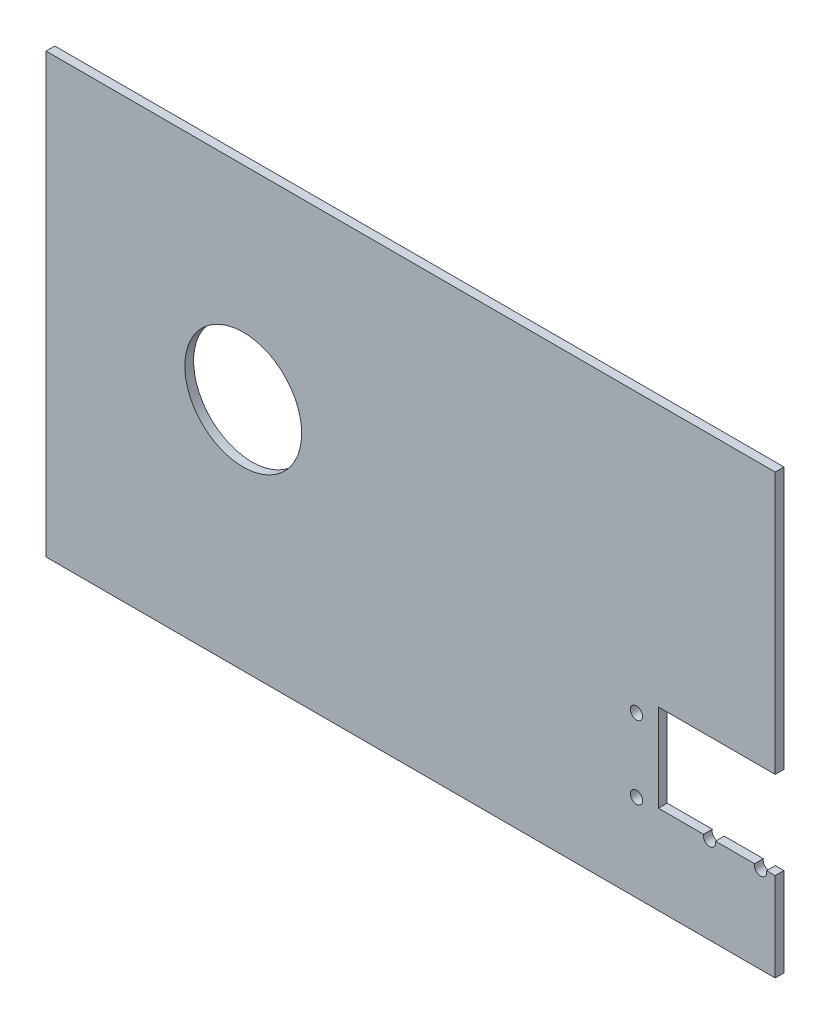
SolidWorks part; units mm, degrees
ref_plane "Front Plane" through (0, 0, 0) normal (0, 0, 1) x (1, 0, 0)
ref_plane "Top Plane" through (0, 0, 0) normal (0, 1, 0) x (1, 0, 0)
ref_plane "Right Plane" through (0, 0, 0) normal (1, 0, 0) x (0, 0, -1)
sketch "Sketch1" plane through (0, 0, 0) normal (0, 0, 1) x (1, 0, 0)
  line L1 (0, 0) -> (249.6, 0)
  line L2 (0, 0) -> (0, -150)
  line L3 (0, -150) -> (249.6, -150)
  line L4 (249.6, 0) -> (249.6, -150)
  dimension "D1" = 150
  dimension "D2" = 249.6
extrude "Boss-Extrude1" add sketch "Sketch1" along normal blind 3
sketch "Sketch2" plane through (0, 0, 3) normal (0, 0, 1) x (1, 0, 0)
  circle A0 centre (67.5, -69.5849) radius 20
  dimension "D1" = 40
extrude "Cut-Extrude1" cut sketch "Sketch2" against normal through all
sketch "Sketch3" plane through (0, 0, 3) normal (0, 0, 1) x (1, 0, 0)
  line L0 (249.6, -89.6523) -> (195.8, -89.6523) construction
  line L1 (209.6, -89.6523) -> (249.6, -89.6523)
  line L2 (209.6, -89.6523) -> (209.6, -119.6523)
  line L3 (209.6, -119.6523) -> (249.6, -119.6523)
  line L4 (249.6, -89.6523) -> (249.6, -119.6523)
  line L5 (249.6, -150) -> (249.6, 0) construction
  dimension "D1" = 30
  dimension "D2" = 40
extrude "Cut-Extrude2" cut sketch "Sketch3" against normal blind 5
sketch "Sketch4" plane through (0, 0, 3) normal (0, 0, 1) x (1, 0, 0)
  circle A0 centre (244.6, -120.1523) radius 2.1
  circle A1 centre (227.1, -120.1523) radius 2.1
  circle A2 centre (239.6, -107.6523) radius 4
  circle A3 centre (244.6, -95.1523) radius 2.1
  circle A4 centre (227.1, -95.1523) radius 2.1
  circle A5 centre (202.1, -120.1523) radius 2.1
  circle A8 centre (202.1, -95.1523) radius 2.1
  circle A9 centre (244.6, -120.1523) radius 2.1 construction
  circle A10 centre (239.6, -107.6523) radius 4 construction
  circle A11 centre (227.1, -120.1523) radius 2.1 construction
  circle A12 centre (202.1, -95.1523) radius 2.1 construction
  circle A13 centre (227.1, -95.1523) radius 2.1 construction
  circle A14 centre (202.1, -120.1523) radius 2.1 construction
  circle A16 centre (214.6, -107.6523) radius 4
  circle A17 centre (214.6, -107.6523) radius 4 construction
  circle A18 centre (244.6, -95.1523) radius 2.1 construction
extrude "Cut-Extrude3" cut sketch "Sketch4" against normal through all
